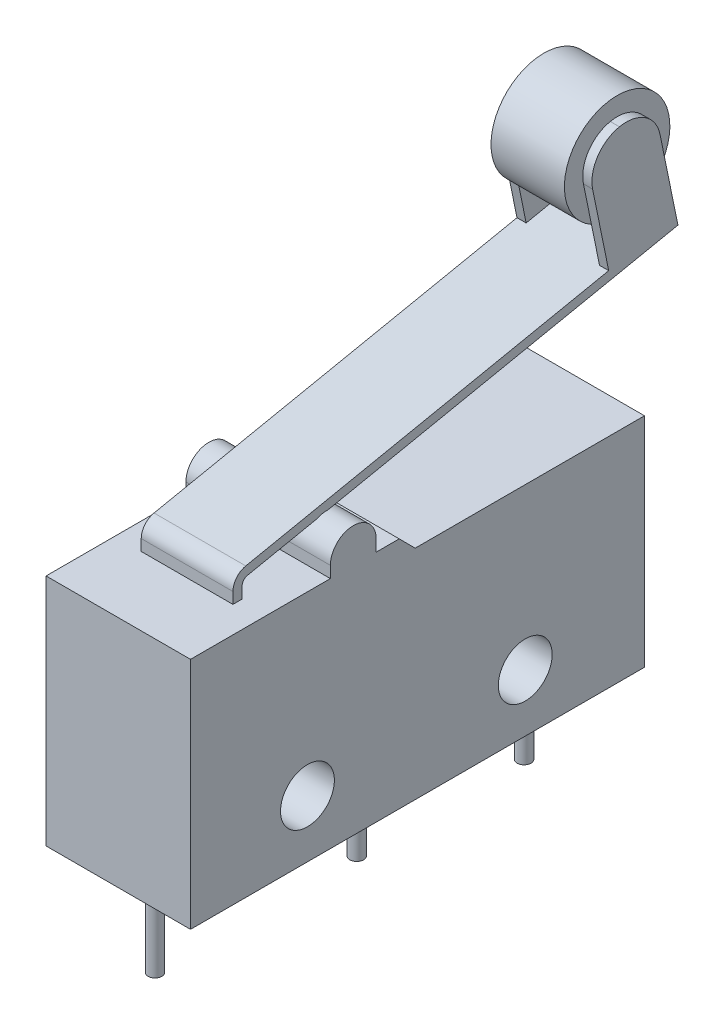
SolidWorks part; units mm, degrees
ref_plane "Plan de face" through (0, 0, 0) normal (0, 0, 1) x (1, 0, 0)
ref_plane "Plan de dessus" through (0, 0, 0) normal (0, 1, 0) x (1, 0, 0)
ref_plane "Plan de droite" through (0, 0, 0) normal (1, 0, 0) x (0, 0, -1)
sketch "Esquisse1" plane through (0, 0, 0) normal (1, 0, 0) x (0, 0, -1)
  line L0 (-20.9804, 0) -> (48.4649, 0) construction
  line L1 (0, -28.8084) -> (0, 30.2165) construction
  line L2 (19.8, 30.2165) -> (19.8, -28.8084) construction
  line L3 (-20.9804, 10.2) -> (15.9251, 10.2) construction
  line L4 (48.4649, 9.5) -> (5.7332, 9.5) construction
  line L5 (5.1, 4.1698) -> (5.1, -14.8554) construction
  line L6 (14.6, -14.8554) -> (14.6, 14.7432) construction
  line L7 (-6.8326, 2.5) -> (18.5008, 2.5) construction
  line L8 (9.8, 12.4461) -> (9.8, 8.308) construction
  line L9 (9.8, 9.5) -> (8.1618, 11.1382) construction
  line L10 (7.1, 14.7432) -> (7.1, 7.1092) construction
  line L11 (6.1, 14.7432) -> (6.1, 7.1092) construction
  line L12 (9.8, 9.5) -> (19.8, 9.5)
  line L13 (19.8, 9.5) -> (19.8, 0)
  line L14 (19.8, 0) -> (0, 0)
  line L15 (0, 0) -> (0, 10.2)
  line L16 (0, 10.2) -> (6.1, 10.2)
  line L17 (9.1025, 10.2) -> (9.8, 9.5)
  line L18 (4.2025, 11.7) -> (8.706, 11.7) construction
  line L19 (4.93, 10.7) -> (8.264, 10.7) construction
  line L20 (6.1, 10.7) -> (6.1, 10.2)
  line L21 (8.1, 10.7) -> (8.1, 10.2)
  line L22 (8.1, 10.2) -> (9.1025, 10.2)
  circle A0 centre (14.6, 2.5) radius 1.175
  circle A1 centre (5.1, 2.5) radius 1.175
  arc A2 (8.1, 10.7) -> (6.1, 10.7) centre (7.1, 10.7) ccw
  dimension "D7" = 7.5
  dimension "D1" = 19.8
  dimension "D2" = 10.2
  dimension "D3" = 9.5
  dimension "D4" = 2.5
  dimension "D5" = 5.1
  dimension "D6" = 9.5
  dimension "D8" = 1
  dimension "D9" = 1.5
  dimension "D10" = 1
extrude "Extrusion1" add sketch "Esquisse1" along normal blind 6.3
sketch "Esquisse2" plane through (0, 0, 0) normal (0, -1, 0) x (1, 0, 0)
  line L0 (-0.9916, 0) -> (10.1412, 0) construction
  line L1 (0, 4.6012) -> (0, -20.6102) construction
  line L2 (3.15, 2.5912) -> (3.15, -20.417) construction
  line L3 (-1.3055, -1.6) -> (10.1412, -1.6) construction
  line L4 (-0.9916, -10.4) -> (10.1412, -10.4) construction
  line L5 (-0.9916, -17.7) -> (10.1412, -17.7) construction
  circle A0 centre (3.15, -1.6) radius 0.3
  circle A1 centre (3.15, -10.4) radius 0.3
  circle A2 centre (3.15, -17.7) radius 0.3
  dimension "D1" = 3.15
  dimension "D2" = 1.6
  dimension "D3" = 8.8
  dimension "D4" = 7.3
extrude "Extrusion2" add sketch "Esquisse2" along normal blind 4
ref_plane "Plan1" through (3.15, 0, 0) normal (1, 0, 0) x (0, 0, -1)
sketch "Esquisse7" plane through (0, 10.2, 0) normal (0, 1, 0) x (-1, 0, 0)
  line L0 (1.6734, 0) -> (-7.2688, 0) construction
  line L1 (0, 0.8363) -> (0, -25.5669) construction
  line L2 (-1.15, 0.8363) -> (-1.15, -3.7442) construction
  line L3 (0.621, -3) -> (-7.2688, -3) construction
  line L4 (0.621, -3.4) -> (-7.2688, -3.4) construction
  line L5 (-3.15, 0.8363) -> (-3.15, -5.6747) construction
  line L6 (-1.15, -3.2) -> (-3.15, -3.2) construction
  line L8 (-1.15, -3) -> (-5.15, -3)
  line L9 (-1.15, -3) -> (-1.15, -3.4)
  line L10 (-1.15, -3.4) -> (-5.15, -3.4)
  line L11 (-5.15, -3) -> (-5.15, -3.4)
  dimension "D1" = 3.15
  dimension "D2" = 2
  dimension "D3" = 3
  dimension "D4" = 0.4
  dimension "D5" = 0.2
sketch "Esquisse8" plane through (3.15, 0, 0) normal (1, 0, 0) x (0, 0, -1)
  line L0 (3.2, 10.2) -> (3.2, 19.5423) construction
  line L1 (23.4823, 9.5) -> (15.8831, 9.5) construction
  line L2 (23.4823, 14.5) -> (15.8831, 14.5) construction
  line L3 (5.1, 5.8578) -> (5.1, -12.0401) construction
  line L4 (20.9, 20.7561) -> (20.9, -12.0401) construction
  line L5 (19.8, 13.0712) -> (19.8, 14.8001) construction
  line L6 (22.7518, 13.1432) -> (20.6903, 23.2203) construction
  line L7 (2.1923, 10.8893) -> (23.4823, 15.2446) construction
  line L8 (20.8998, 14.7124) -> (19.6111, 21.0117) construction
  line L9 (3.2, 10.2) -> (3.2, 10.6874)
  line L10 (3.5998, 11.1772) -> (22.3686, 15.0168)
  arc A0 (3.2, 10.6874) -> (3.5998, 11.1772) centre (3.7, 10.6874) cw
  dimension "D4" = 0.5
  dimension "D1" = 5
  dimension "D2" = 15.8
  dimension "D3" = 1.5
sweep "Balayage1" add profiles "Esquisse7" path "Esquisse8"
sketch "Esquisse9" plane through (0, 10.2174, 2.0902) normal (0, 0.9797, 0.2004) x (-1, 0, 0)
  line L0 (-1.15, -25.4403) -> (-1.15, -21.8588) construction
  line L1 (-0.3289, -24.9244) -> (-6.1357, -24.9244) construction
  line L2 (-3.15, -25.4403) -> (-3.15, -21.8588) construction
  line L3 (-1.55, -25.3625) -> (-1.55, -21.0913) construction
  line L4 (-0.0735, -21.9244) -> (-4.1039, -21.9244) construction
  line L5 (-5.15, -24.9244) -> (-4.75, -24.9244)
  line L6 (-1.15, -24.9244) -> (-1.55, -24.9244)
  line L7 (-1.15, -24.9244) -> (-1.15, -21.9244)
  line L8 (-1.15, -21.9244) -> (-1.55, -21.9244)
  line L9 (-1.55, -24.9244) -> (-1.55, -21.9244)
  line L10 (-4.75, -24.9244) -> (-4.75, -21.9244)
  line L11 (-5.15, -24.9244) -> (-5.15, -21.9244)
  line L12 (-5.15, -21.9244) -> (-4.75, -21.9244)
  dimension "D1" = 3
  dimension "D2" = 0.4
  dimension "D3" = 2
extrude "Extrusion3" add sketch "Esquisse9" along normal blind 5
fillet "Congé1" radius 1.499 4 edges at (1.35, 19.51, -18.3872) (1.35, 20.1113, -21.3264) (4.95, 20.1113, -21.3264) (4.95, 19.51, -18.3872)
sketch "Esquisse10" plane through (1.55, 0, 0) normal (1, 0, 0) x (0, 0, -1)
  line L0 (21.6268, 18.6427) -> (18.6877, 18.0414) construction
  line L1 (19.8578, 19.8108) -> (20.3497, 17.4063) construction
  circle A0 centre (20.1572, 18.3421) radius 2.3
extrude "Extrusion4" add sketch "Esquisse10" along normal blind 3.2
